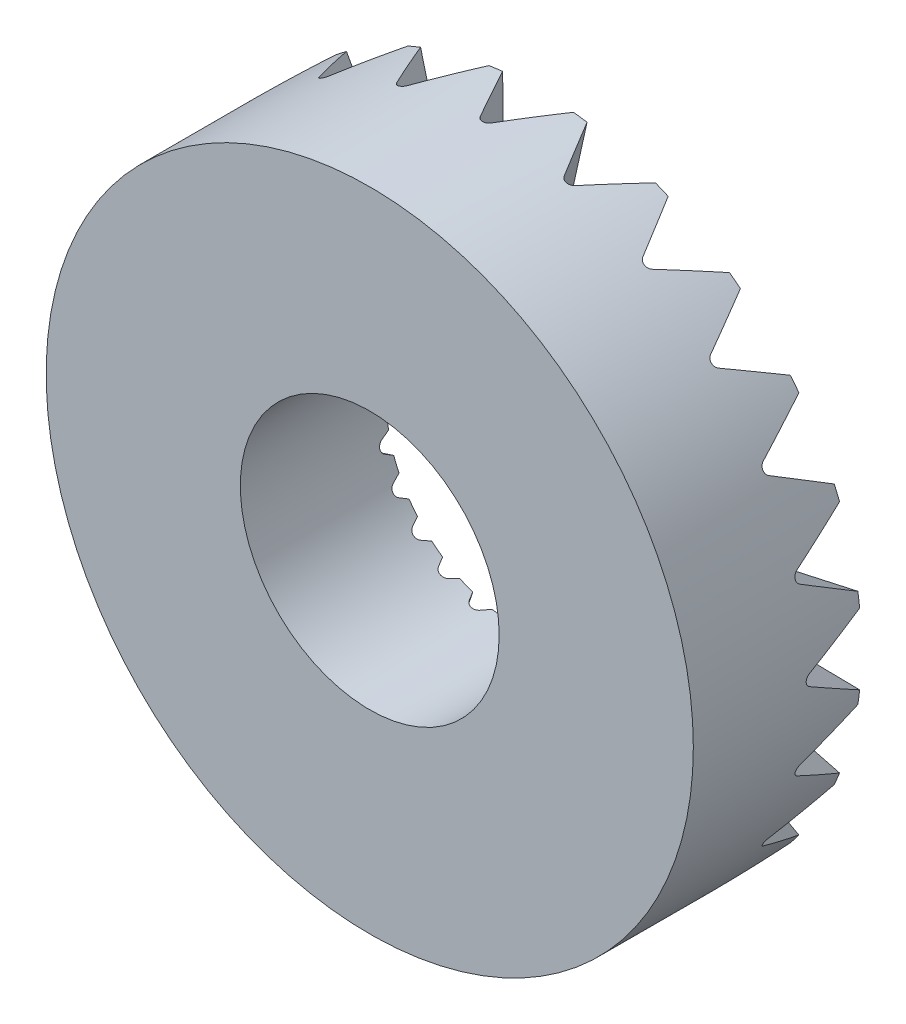
SolidWorks part; units mm, degrees
material "Rostfreier Chromstahl"
ref_plane "Ebene vorne" through (0, 0, 0) normal (0, 0, 1) x (1, 0, 0)
ref_plane "Ebene oben" through (0, 0, 0) normal (0, 1, 0) x (1, 0, 0)
ref_plane "Ebene rechts" through (0, 0, 0) normal (1, 0, 0) x (0, 0, -1)
sketch "Skizze1" plane through (0, 0, 0) normal (1, 0, 0) x (0, 0, -1)
  line L0 (0, 0) -> (61.1854, 0) construction
  line L1 (0, 10) -> (0, 25)
  line L2 (0, 25) -> (13, 25)
  line L3 (13, 25) -> (11.2856, 10)
  line L4 (11.2856, 10) -> (0, 10)
  dimension "D1" = 20
  dimension "D2" = 50
  dimension "D3" = 13
  dimension "D4" = 83.48
revolve "Rotation1" add sketch "Skizze1" angle 360 about L0
sketch "Skizze2" plane through (0, 0, 0) normal (1, 0, 0) x (0, 0, -1)
  line L1 (6.5, 25) -> (6.5, -25) construction
  line L2 (13, 25) -> (0, 25) construction
  line L3 (0, -25) -> (13, -25) construction
ref_plane "Ebene1" through (-0.7333, 0, -0.0838) normal (0.9935, 0, 0.1136) x (0.1136, 0, -0.9935)
sketch "Skizze3" plane through (-0.7333, 0, -0.0838) normal (0.9935, 0, 0.1136) x (0.1136, 0, -0.9935)
  line L0 (0, 0) -> (25.2384, 0) construction
  line L1 (19.6603, 5) -> (11.75, 0.433)
  line L2 (11.75, -0.433) -> (19.6603, -5)
  line L3 (19.6603, -5) -> (19.6603, 5)
  arc A0 (11.75, 0.433) -> (11.75, -0.433) centre (12, 0) ccw
  point P8 (11, 0)
  dimension "D2" = 0.5
  dimension "D1" = 60
  dimension "D3" = 10
  dimension "D4" = 12
extrude "Schnitt-Linear austragen1" cut sketch "Skizze3" along normal through all
pattern_circular "Kreismuster1" count 24 over 360 about axis through (0, 0, 0) along (0, 0, 1) of "Schnitt-Linear austragen1"
